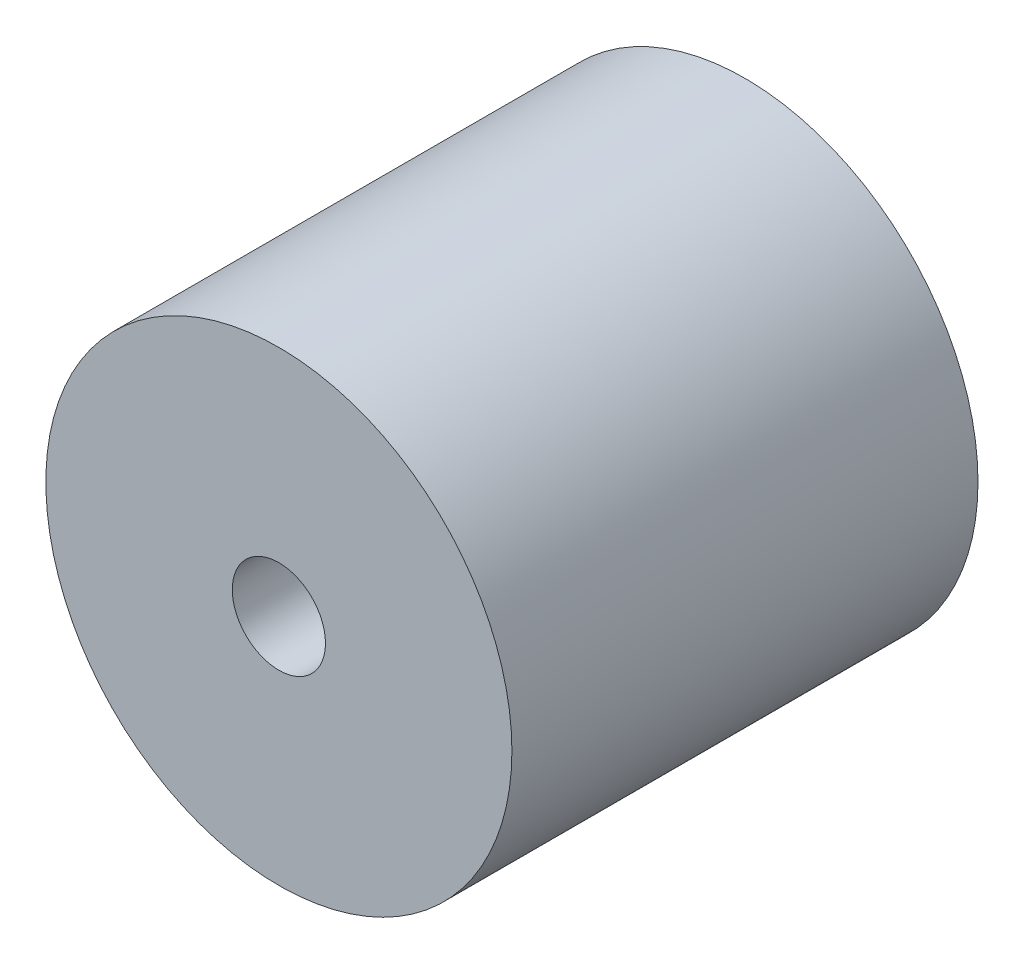
SolidWorks part; units mm, degrees
ref_plane "Front Plane" through (0, 0, 0) normal (0, 0, 1) x (1, 0, 0)
ref_plane "Top Plane" through (0, 0, 0) normal (0, 1, 0) x (1, 0, 0)
ref_plane "Right Plane" through (0, 0, 0) normal (1, 0, 0) x (0, 0, -1)
sketch "Croquis1" plane through (0, 0, 0) normal (0, 0, 1) x (1, 0, 0)
  circle A0 centre (0, 0) radius 0.1
  circle A1 centre (0, 0) radius 0.5
  dimension "D1" = 0.2
  dimension "D2" = 1
extrude "Saliente-Extruir1" add sketch "Croquis1" along normal blind 1
